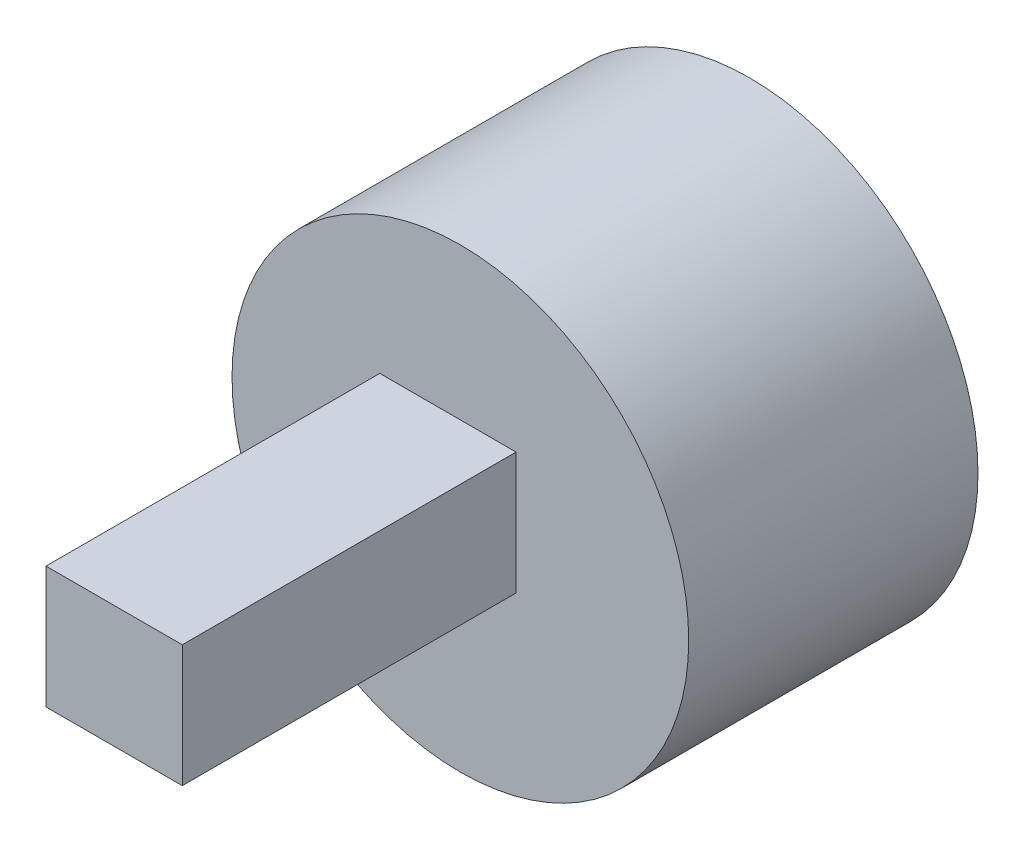
SolidWorks part; units mm, degrees
material "ASTM A36 Steel"
ref_plane "Front Plane" through (0, 0, 0) normal (0, 0, 1) x (1, 0, 0)
ref_plane "Top Plane" through (0, 0, 0) normal (0, 1, 0) x (1, 0, 0)
ref_plane "Right Plane" through (0, 0, 0) normal (1, 0, 0) x (0, 0, -1)
sketch "Sketch1" plane through (0, 0, 0) normal (0, 0, 1) x (1, 0, 0)
  circle A0 centre (0, 0) radius 20.5227
extrude "Boss-Extrude1" add sketch "Sketch1" along normal blind 26
sketch "Sketch2" plane through (0, 0, 26) normal (0, 0, 1) x (1, 0, 0)
  line L1 (-7.2438, -4.0724) -> (5.0045, -4.0724)
  line L2 (-7.2438, -4.0724) -> (-7.2438, 6.8962)
  line L3 (-7.2438, 6.8962) -> (5.0045, 6.8962)
  line L4 (5.0045, -4.0724) -> (5.0045, 6.8962)
  line L5 (-7.2438, -4.0724) -> (5.0045, 6.8962) construction
  line L6 (-7.2438, 6.8962) -> (5.0045, -4.0724) construction
  point P0 (-1.1196, 1.4119)
extrude "Boss-Extrude2" add sketch "Sketch2" along normal blind 30
